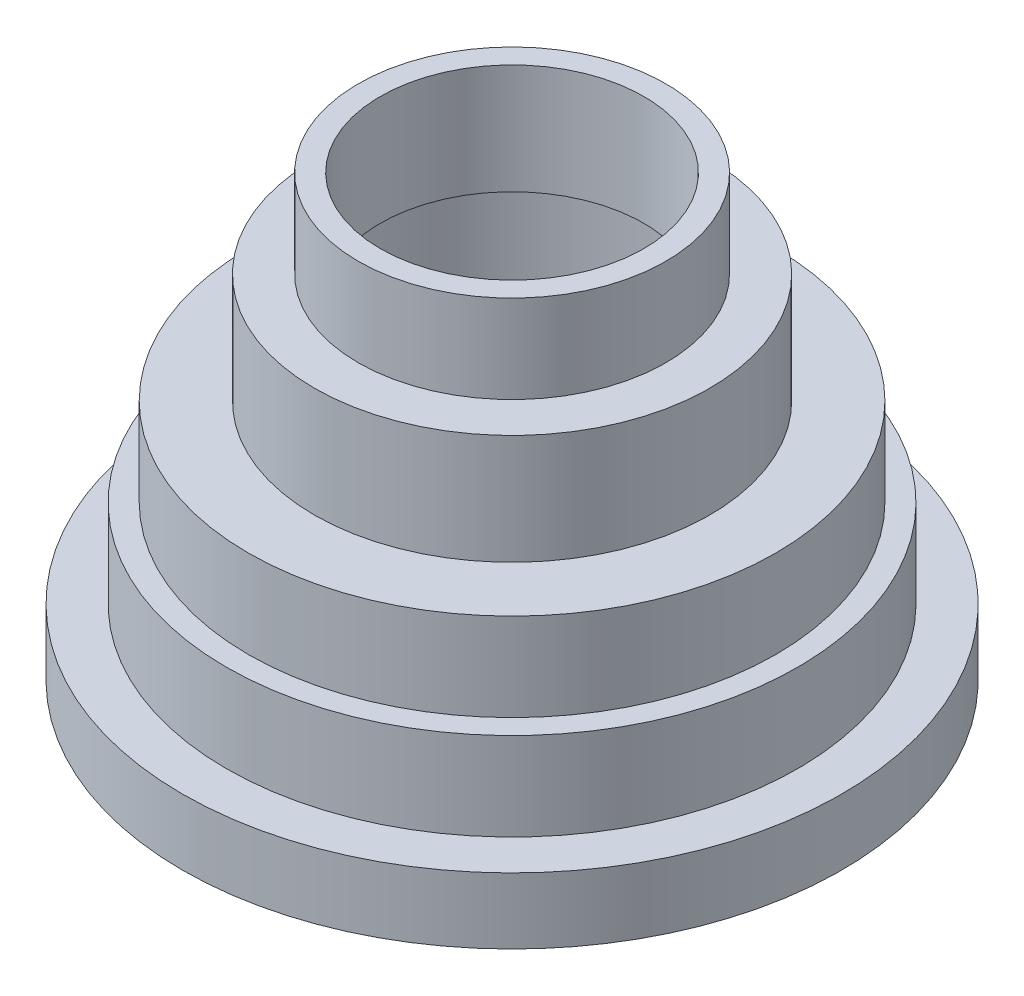
SolidWorks part; units mm, degrees
ref_plane "Front Plane" through (0, 0, 0) normal (0, 0, 1) x (1, 0, 0)
ref_plane "Top Plane" through (0, 0, 0) normal (0, 1, 0) x (1, 0, 0)
ref_plane "Right Plane" through (0, 0, 0) normal (1, 0, 0) x (0, 0, -1)
sketch "Sketch1" plane through (0, 0, 0) normal (0, 0, 1) x (1, 0, 0)
  line L0 (0, 50) -> (0, -50) construction
  line L1 (-75, -49.4037) -> (-75, -34.4037)
  line L2 (-75, -34.4037) -> (-65, -34.4037)
  line L3 (-65, -34.4037) -> (-65, -14.4037)
  line L4 (-65, -14.4037) -> (-60, -14.4037)
  line L5 (-60, -14.4037) -> (-60, 5.5963)
  line L6 (-60, 5.5963) -> (-45, 5.5963)
  line L7 (-45, 5.5963) -> (-45, 30.5963)
  line L8 (-45, 30.5963) -> (-35, 30.5963)
  line L9 (-35, 30.5963) -> (-35, 50.5963)
  line L10 (-70, -49.4037) -> (-70, -39.4037)
  line L11 (-70, -39.4037) -> (-60, -39.4037)
  line L12 (-60, -39.4037) -> (-60, -19.4037)
  line L13 (-60, -19.4037) -> (-55, -19.4037)
  line L14 (-55, -19.4037) -> (-55, 0.5963)
  line L15 (-55, 0.5963) -> (-40, 0.5963)
  line L16 (-40, 0.5963) -> (-40, 25.5963)
  line L17 (-40, 25.5963) -> (-30, 25.5963)
  line L18 (-30, 25.5963) -> (-30, 50.5963)
  line L19 (-35, 50.5963) -> (-30, 50.5963)
  line L20 (-75, -49.4037) -> (-70, -49.4037)
  point P4 (0, 0)
  dimension "D1" = 100
  dimension "D2" = 75
  dimension "D3" = 15
  dimension "D4" = 20
  dimension "D5" = 20
  dimension "D6" = 25
  dimension "D7" = 20
  dimension "D8" = 10
  dimension "D9" = 5
  dimension "D10" = 15
  dimension "D11" = 10
  dimension "D12" = 5
revolve "Revolve1" add sketch "Sketch1" angle 360 about L0
